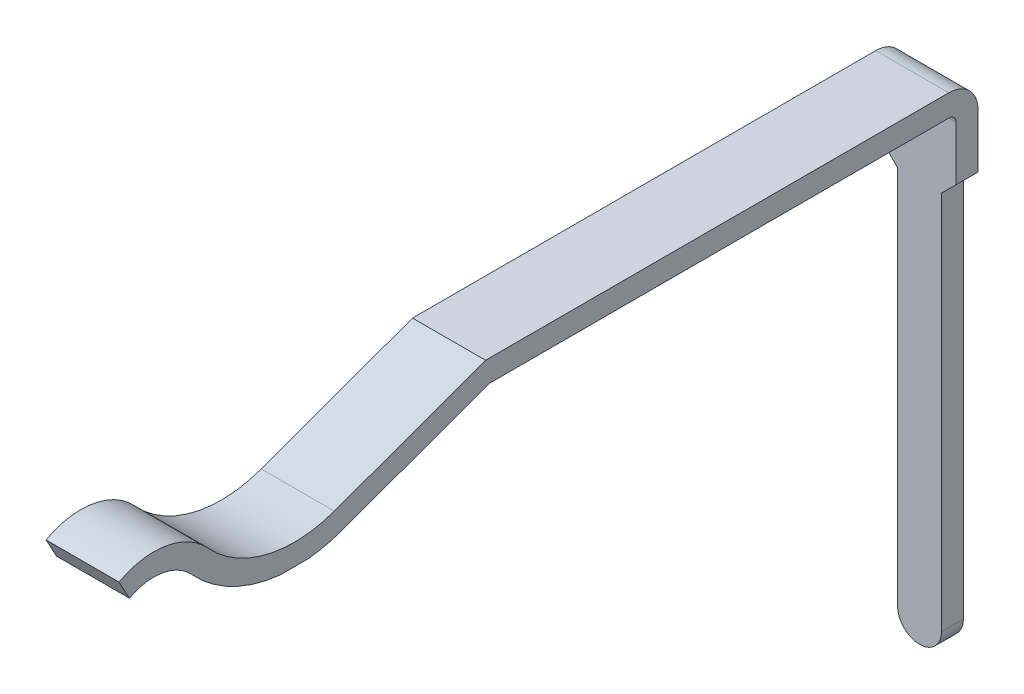
SolidWorks part; units mm, degrees
material "Pure Gold"
ref_plane "Front Plane" through (0, 0, 0) normal (0, 0, 1) x (1, 0, 0)
ref_plane "Top Plane" through (0, 0, 0) normal (0, 1, 0) x (1, 0, 0)
ref_plane "Right Plane" through (0, 0, 0) normal (1, 0, 0) x (0, 0, -1)
sketch "Sketch1" plane through (0, 0, 0) normal (1, 0, 0) x (0, 0, -1)
  line L0 (0, -0.75) -> (36.8303, -0.75) construction
  line L1 (55, 0) -> (-55, 0) construction
  line L2 (0, 55) -> (0, -55) construction
  line L3 (3.4, -0.85) -> (3.4, -0.75) construction
  line L4 (6.0175, 0) -> (12.36, 0)
  line L5 (12.76, -0.4) -> (12.76, -6.84)
  line L7 (6.0175, 0) -> (3.9472, -0.7535)
  arc A1 (12.36, 0) -> (12.76, -0.4) centre (12.36, -0.4) cw
  arc A3 (3.9472, -0.7535) -> (2.2167, -0.3269) centre (3.4, 0.75) cw
  arc A4 (2.2167, -0.3269) -> (1, -0.1212) centre (1.4771, -1) ccw
  dimension "D4" = 1
  dimension "D6" = 3.4
  dimension "D9" = 0.4
  dimension "D7" = 1
  dimension "D3" = 0.75
  dimension "D1" = 0.75
  dimension "D2" = 0.1
  dimension "D8" = 12.76
  dimension "D10" = 6.84
  dimension "D11" = 20
extrude "Extrude-Thin1" add sketch "Sketch1" along normal mid plane 1 thin
sketch "Sketch2" plane through (0, 0, 0) normal (0, 0, 1) x (1, 0, 0)
  line L0 (0, -4.686) -> (0, 4.686) construction
  line L1 (0.5, -6.84) -> (-0.5, -6.84) construction
  line L2 (-0.3, -6.54) -> (-0.3, -1.34)
  line L3 (-0.3, -1.34) -> (-0.5, -1.14)
  line L4 (-0.5, -0.4) -> (-0.5, -6.84) construction
  line L5 (-0.5, -1.14) -> (-0.5, -7.54)
  line L6 (-0.5, -7.54) -> (0.5, -7.54)
  line L7 (0.5, -7.54) -> (0.5, -1.14)
  line L8 (0.5, -0.4) -> (0.5, -6.84) construction
  line L9 (0.5, -1.14) -> (0.3, -1.34)
  line L10 (0.3, -1.34) -> (0.3, -6.54)
  arc A0 (-0.3, -6.54) -> (0.3, -6.54) centre (0, -6.54) ccw
  dimension "D1" = 0.6
  dimension "D2" = 0.3
  dimension "D3" = 5.5
  dimension "D4" = 1
  dimension "D5" = 45
extrude "Cut-Extrude1" cut sketch "Sketch2" against normal through all
